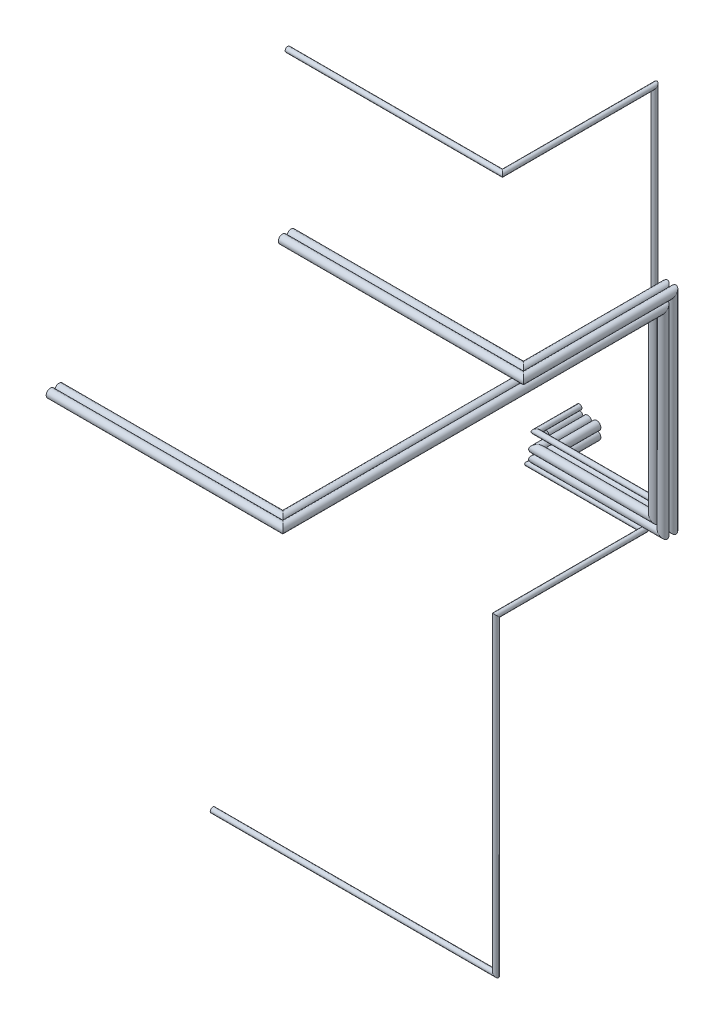
SolidWorks part; units mm, degrees
ref_plane "Front Plane" through (0, 0, 0) normal (0, 0, 1) x (1, 0, 0)
ref_plane "Top Plane" through (0, 0, 0) normal (0, 1, 0) x (1, 0, 0)
ref_plane "Right Plane" through (0, 0, 0) normal (1, 0, 0) x (0, 0, -1)
sketch "Sketch1" plane through (0, 0, 0) normal (0, 0, 1) x (1, 0, 0)
  circle A0 centre (0, 0) radius 50
  circle A1 centre (104.6203, 0) radius 50
  circle A3 centre (104.6203, 101.6323) radius 50
  circle A5 centre (0, 101.6323) radius 50
  circle A6 centre (209.2405, 0) radius 50 [skipped]
  circle A7 centre (209.2405, 101.6323) radius 50 [skipped]
  dimension "D1" = 3
  dimension "D2" = 2
sketch3d "3DSketch1"
  line L0 (0, 0, 0) -> (0, 0, 600)
  line L1 (0, 0, 600) -> (1490, 0, 600)
  line L2 (1490, 0, 600) -> (1490, 2300, 600)
  line L3 (1490, 2300, 600) -> (1490, 2300, 2000)
  dimension "D1" = 600
  dimension "D2" = 1400
  dimension "D3" = 2300
  dimension "D4" = 1490
sweep "Sweep1" add profiles "Sketch1" path "3DSketch1"
sketch "Sketch2" plane through (0, 0, 2000) normal (0, 0, 1) x (1, 0, 0)
  circle A1 centre (1490, 2404.6203) radius 50
  circle A2 centre (1388.3677, 2404.6203) radius 50
sketch3d "3DSketch2"
  line L0 (1388.3677, 2404.6203, 2000) -> (1388.3677, 2404.6203, 2150)
  line L1 (1388.3677, 2404.6203, 2150) -> (-1361.6323, 2404.6203, 2150)
  dimension "D1" = 150
  dimension "D2" = 2750
sketch "Sketch3" plane through (0, 0, 2000) normal (0, 0, 1) x (1, 0, 0)
  circle A0 centre (1490, 2300) radius 50
  circle A2 centre (1388.3677, 2300) radius 50
sketch3d "3DSketch3"
  line L0 (1490, 2300, 2000) -> (1490, 2300, 5100)
  line L1 (1490, 2300, 5100) -> (-1260, 2300, 5100)
  circle A1 centre (1490, 2300, 2000) radius 50 construction
  point P5 (1490, 2300, 2050)
  dimension "D1" = 2750
  dimension "D2" = 3100
sketch "Sketch4" plane through (0, 0, 0) normal (0, 0, -1) x (-1, 0, 0)
  circle A0 centre (104.9294, 0) radius 50
  circle A1 centre (104.9294, 105) radius 50
  dimension "D1" = 100
  dimension "D2" = 100
  dimension "D3" = 105
extrude "Boss-Extrude1" add sketch "Sketch4" against normal blind 400 separate body
sketch "Sketch5" plane through (0, 0, 0) normal (0, 0, -1) x (-1, 0, 0)
  circle A1 centre (99.2922, -103.9964) radius 30
  dimension "D2" = 60
sketch3d "3DSketch5"
  line L0 (-99.2922, -103.9964, 0) -> (-99.2922, -103.9964, 587.6533)
  line L1 (-99.2922, -103.9964, 587.6533) -> (1250.7078, -103.9964, 587.6533)
  line L2 (1250.7078, -103.9964, 587.6533) -> (1250.7078, -103.9964, 2337.6533)
  line L3 (1250.7078, -3775.4046, 2337.6533) -> (-2100.968, -3775.4046, 2337.6533)
  line L4 (1250.7078, -103.9964, 2337.6533) -> (1250.7078, -3775.4046, 2337.6533)
  dimension "D1" = 1750
  dimension "D2" = 1350
sweep "Sweep6" add profiles "Sketch5" path "3DSketch5"
sketch "Sketch7" plane through (0, 0, 0) normal (0, 0, -1) x (-1, 0, 0)
  circle A0 centre (99.2922, 188.1121) radius 30
sketch3d "3DSketch4"
  line L0 (-99.2922, 188.1121, 0) -> (-99.2922, 188.1121, 510.9908)
  line L3 (-99.2922, 188.1121, 510.9908) -> (1300.7078, 188.1121, 510.9908)
  line L4 (1300.7078, 188.1121, 510.9908) -> (1300.7078, 4438.1121, 510.9908)
  line L5 (1300.7078, 4438.1121, 510.9908) -> (1300.7078, 4438.1121, 2310.9908)
  line L6 (1300.7078, 4438.1121, 2310.9908) -> (-1240.4261, 4438.1121, 2310.9908)
  point P1 (0, 0, 0)
  dimension "D1" = 4250
  dimension "D2" = 1800
  dimension "D3" = 1400
sweep "Sweep8" add profiles "Sketch7" path "3DSketch4"
sweep "Sweep9" add profiles "Sketch3" path "3DSketch3"
sweep "Sweep10" add profiles "Sketch2" path "3DSketch2"
